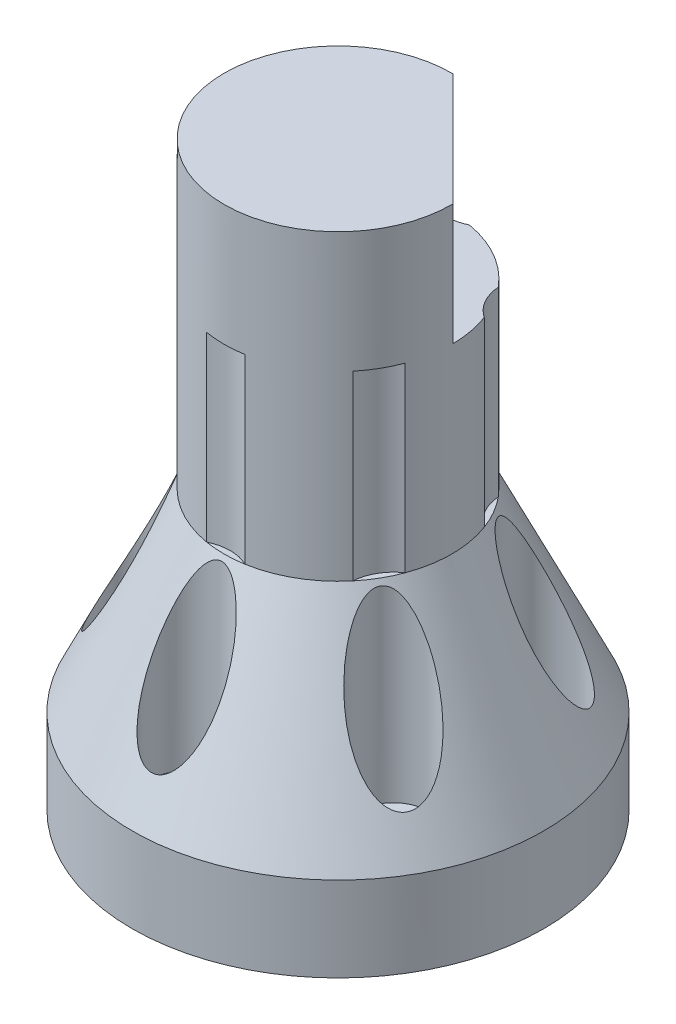
SolidWorks part; units mm, degrees
other "标注1"
sketch "草图20" plane through (-40, 128, 27.5) normal (-0.9349, 0.1755, 0.3084) x (0.3368, 0.1651, 0.927)
other "标注2"
sketch "草图32" plane through (-17, 40, 17) normal (-0.2707, 0.3432, 0.8994) x (-0.2621, -0.9253, 0.2742)
ref_plane "前视基准面" through (0, 0, 0) normal (0, 0, 1) x (1, 0, 0)
ref_plane "上视基准面" through (0, 0, 0) normal (0, 1, 0) x (1, 0, 0)
ref_plane "右视基准面" through (0, 0, 0) normal (1, 0, 0) x (0, 0, -1)
other "Configuration Table"
sketch "草图25" plane through (0, 0, 0) normal (0, 1, 0) x (1, 0, 0)
  circle A0 centre (0, 0) radius 17
  circle A2 centre (0, 12.5) radius 1.65
  circle A3 centre (10.8253, 6.25) radius 1.65
  circle A4 centre (10.8253, -6.25) radius 1.65
  circle A5 centre (0, -12.5) radius 1.65
  circle A6 centre (-10.8253, -6.25) radius 1.65
  circle A7 centre (-10.8253, 6.25) radius 1.65
  point P17 (0, 0)
  dimension "D1" = 6
extrude "凸台-拉伸1" add sketch "草图25" along normal blind 7
ref_plane "基准面1" through (0, 38, 0) normal (0, 1, 0) x (1, 0, 0)
sketch "草图26" plane through (0, 38, 0) normal (0, 1, 0) x (1, 0, 0)
  arc A13 (1.7276, -9.3416) -> (7.2263, -6.1669) centre (0, 0) ccw
  arc A20 (-1.7276, 9.3416) -> (1.7276, 9.3416) centre (0, 12.5) ccw
  arc A21 (7.2263, 6.1669) -> (8.9538, 3.1747) centre (10.8253, 6.25) ccw
  arc A22 (8.9538, -3.1747) -> (7.2263, -6.1669) centre (10.8253, -6.25) ccw
  arc A23 (1.7276, -9.3416) -> (-1.7276, -9.3416) centre (0, -12.5) ccw
  arc A24 (-7.2263, -6.1669) -> (-8.9538, -3.1747) centre (-10.8253, -6.25) ccw
  arc A25 (-8.9538, 3.1747) -> (-7.2263, 6.1669) centre (-10.8253, 6.25) ccw
  arc A26 (-7.2263, -6.1669) -> (-1.7276, -9.3416) centre (0, 0) ccw
  arc A27 (8.9538, -3.1747) -> (8.9538, 3.1747) centre (0, 0) ccw
  arc A28 (7.2263, 6.1669) -> (1.7276, 9.3416) centre (0, 0) ccw
  arc A29 (-1.7276, 9.3416) -> (-7.2263, 6.1669) centre (0, 0) ccw
  arc A30 (-8.9538, 3.1747) -> (-8.9538, -3.1747) centre (0, 0) ccw
  point P17 (0, 0)
  point P19 (0.0373, 0.0441)
  dimension "D1" = 6
extrude "凸台-拉伸2" add sketch "草图26" against normal blind 15 separate body contours A30 A24 A26 A23 A13 A22 A27 A21 A28 A20 A29 A25
sketch "草图28" plane through (0, 7, 0) normal (0, 1, 0) x (1, 0, 0)
  circle A0 centre (0, 0) radius 17
sketch "草图30" plane through (0, 0, 0) normal (0, -1, 0) x (1, 0, 0)
  circle A1 centre (-10.2, 0) radius 2.15
  circle A2 centre (5.1, 8.8335) radius 2.15
  circle A3 centre (5.1, -8.8335) radius 2.15
  point P8 (0, 0)
  dimension "D1" = 3
sketch "草图33" plane through (0, 23, 0) normal (0, -1, 0) x (1, 0, 0)
  circle A0 centre (0, 0) radius 9.4
loft "放样1" add profiles "草图28", "草图33"
extrude "切除-拉伸1" cut sketch "草图30" against normal blind 3
sketch "草图34" plane through (0, 7, 0) normal (0, -1, 0) x (1, 0, 0)
  circle A0 centre (0, 12.5) radius 2.9
  circle A1 centre (10.8253, 6.25) radius 2.9
  circle A2 centre (10.8253, -6.25) radius 2.9
  circle A3 centre (0, -12.5) radius 2.9
  circle A4 centre (-10.8253, -6.25) radius 2.9
  circle A5 centre (-10.8253, 6.25) radius 2.9
  point P15 (0, 0)
  dimension "D1" = 6
extrude "切除-拉伸2" cut sketch "草图34" against normal through all
sketch "草图35" plane through (0, 38, 0) normal (0, 1, 0) x (1, 0, 0)
  line L0 (0, 9.5) -> (9.5, 0)
  arc A0 (0, 9.5) -> (9.5, 0) centre (0, 0) ccw
extrude "凸台-拉伸3" add sketch "草图35" along normal blind 10
sketch "草图36" plane through (0, 48, 0) normal (0, 1, 0) x (1, 0, 0)
  circle A0 centre (0, 0) radius 9.5
  circle A1 centre (0, 0) radius 9.4
extrude "切除-拉伸3" cut sketch "草图36" against normal up to surface (25 mm away) up to face at (7.2338, 23, -6.0027)
